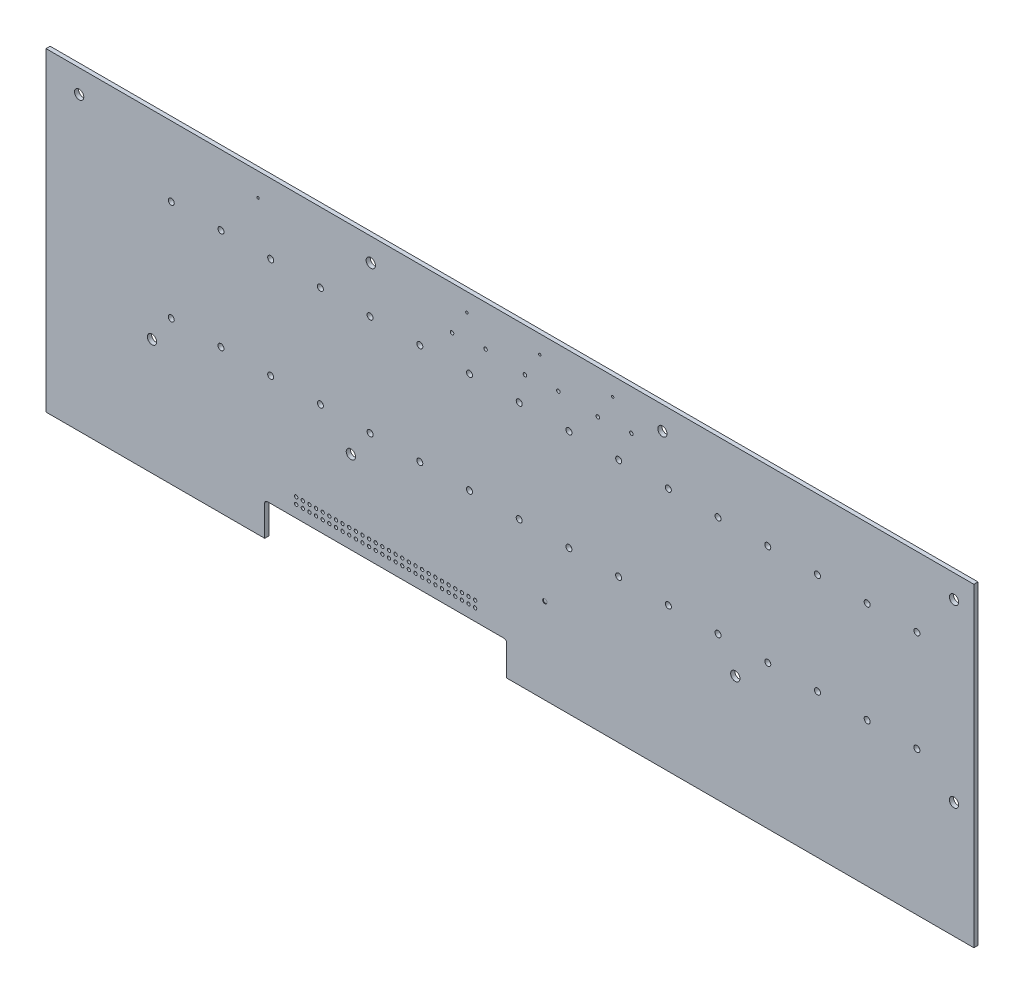
SolidWorks part; units mm, degrees
ref_plane "Front" through (0, 0, 0) normal (0, 0, 1) x (1, 0, 0)
ref_plane "Top" through (0, 0, 0) normal (0, 1, 0) x (1, 0, 0)
ref_plane "Right" through (0, 0, 0) normal (1, 0, 0) x (0, 0, -1)
sketch "Sketch1" plane through (0, 0, 0) normal (0, 0, 1) x (1, 0, 0)
  line L1 (0, 0) -> (355.6, 0)
  line L2 (0, 0) -> (0, -120.65)
  line L3 (0, -120.65) -> (355.6, -120.65)
  line L4 (355.6, 0) -> (355.6, -120.65)
  dimension "D1" = 120.65
  dimension "D2" = 355.6
extrude "Extrude1" add sketch "Sketch1" along normal blind 1.5748
sketch "DSPboard connector holes" plane through (0, 0, 1.5748) normal (0, 0, 1) x (1, 0, 0)
  line L0 (0, -120.65) -> (355.6, -120.65) construction
  line L1 (0, 0) -> (0, -120.65) construction
  circle A0 centre (48.006, -65.532) radius 1.15
  circle A1 centre (48.006, -26.802) radius 1.15
  dimension "D1" = 2.3
  dimension "D4" = 2.3
  dimension "D2" = 55.118
  dimension "D3" = 48.006
  dimension "D5" = 38.73
extrude "Cut-Extrude1" cut sketch "DSPboard connector holes" against normal blind 2.54
pattern_linear "LPattern1" count 16 spacing 19.05 along (1, 0, 0) of "Cut-Extrude1"
sketch "Sketch2" plane through (0, 0, 1.5748) normal (0, 0, 1) x (1, 0, 0)
  line L0 (0, -120.65) -> (355.6, -120.65) construction
  line L1 (0, 0) -> (0, -120.65) construction
  circle A0 centre (12.7, -8.89) radius 1.778
  circle A1 centre (124.46, -8.89) radius 1.778
  circle A2 centre (236.22, -8.89) radius 1.778
  circle A3 centre (347.98, -8.89) radius 1.778
  circle A4 centre (40.64, -76.2) radius 1.778
  circle A5 centre (116.84, -76.2) radius 1.778
  circle A6 centre (264.16, -76.2) radius 1.778
  circle A7 centre (347.98, -76.2) radius 1.778
  dimension "D1" = 3.556
  dimension "D4" = 3.556
  dimension "D5" = 3.556
  dimension "D6" = 3.556
  dimension "D10" = 3.556
  dimension "D11" = 3.556
  dimension "D12" = 3.556
  dimension "D13" = 3.556
  dimension "D2" = 111.76
  dimension "D3" = 12.7
  dimension "D7" = 124.46
  dimension "D8" = 236.22
  dimension "D9" = 347.98
  dimension "D14" = 44.45
  dimension "D15" = 40.64
  dimension "D16" = 116.84
  dimension "D17" = 264.16
  dimension "D18" = 347.98
extrude "PCB Mount holes" cut sketch "Sketch2" against normal blind 2.54
sketch "Sketch6" plane through (0, 0, 1.5748) normal (0, 0, 1) x (1, 0, 0)
  line L1 (0, 0) -> (0, -120.65) construction
  line L2 (355.6, 0) -> (0, 0) construction
  circle A4 centre (168.4383, -15.51) radius 0.675
  circle A5 centre (155.6083, -16.51) radius 0.675
  dimension "D2" = 16.51
  dimension "D8" = 1.35
  dimension "D9" = 1.35
  dimension "D11" = 12.83
  dimension "D14" = 155.6083
extrude "Peripheral-SATA" cut sketch "Sketch6" against normal blind 2.54
sketch "Sketch7" plane through (0, 0, 1.5748) normal (0, 0, 1) x (1, 0, 0)
  line L0 (355.6, 0) -> (0, 0) construction
  line L1 (0, 0) -> (0, -120.65) construction
  circle A0 centre (217.17, -6.985) radius 0.45
  circle A1 centre (189.23, -6.985) radius 0.45
  circle A2 centre (161.29, -6.985) radius 0.45
  circle A3 centre (81.28, -8.89) radius 0.45
  dimension "D1" = 0.9
  dimension "D4" = 0.8999
  dimension "D5" = 0.8999
  dimension "D6" = 0.8999
  dimension "D2" = 27.94
  dimension "D3" = 27.94
  dimension "D8" = 6.985
  dimension "D9" = 8.89
  dimension "D10" = 81.28
  dimension "D11" = 161.29
extrude "Off-board header holes" cut sketch "Sketch7" against normal blind 2.54
sketch "Sketch9" plane through (0, 0, 1.5748) normal (0, 0, 1) x (1, 0, 0)
  line L0 (0, -120.65) -> (355.6, -120.65) construction
  line L1 (84.836, -107.95) -> (175.514, -107.95)
  line L2 (83.82, -108.966) -> (83.82, -120.65)
  line L3 (83.82, -120.65) -> (176.53, -120.65)
  line L4 (176.53, -108.966) -> (176.53, -120.65)
  line L5 (0, 0) -> (0, -120.65) construction
  arc A0 (175.514, -107.95) -> (176.53, -108.966) centre (175.514, -108.966) cw
  arc A1 (83.82, -108.966) -> (84.836, -107.95) centre (84.836, -108.966) cw
  dimension "D1" = 1.016
  dimension "D2" = 1.016
  dimension "D3" = 92.71
  dimension "D4" = 83.82
  dimension "D5" = 12.7
extrude "NIC cutout" cut sketch "Sketch9" against normal blind 2.54
sketch "Sketch10" plane through (0, 0, 1.5748) normal (0, 0, 1) x (1, 0, 0)
  line L2 (175.514, -107.95) -> (84.836, -107.95) construction
  line L3 (176.53, -120.65) -> (176.53, -108.966) construction
  circle A0 centre (164.465, -100.838) radius 0.635
  dimension "D1" = 1.27
  dimension "D2" = 7.112
  dimension "D3" = 12.065
extrude "Header Holes" cut sketch "Sketch10" against normal blind 2.54
sketch "BGA mount pos" plane through (0, 0, 1.5748) normal (0, 0, 1) x (1, 0, 0)
  line L0 (0, 0) -> (0, -120.65) construction
  line L1 (176.53, -120.65) -> (355.6, -120.65) construction
  circle A0 centre (191.2, -87.85) radius 0.8381
  point P0 (191.2, -87.85)
  point P1 (0, -90.4568)
  dimension "D1" = 191.2
  dimension "D2" = 32.8
extrude "Cut-Extrude11" cut sketch "BGA mount pos" against normal blind 0.254
pattern_linear "LPattern3" count 28 spacing 2.54 along (-1, 0, 0) count 2 spacing 2.54 along (0, -1, 0) of "Header Holes"
pattern_linear "LPattern4" count 3 spacing 27.94 along (1, 0, 0) of "Peripheral-SATA"
